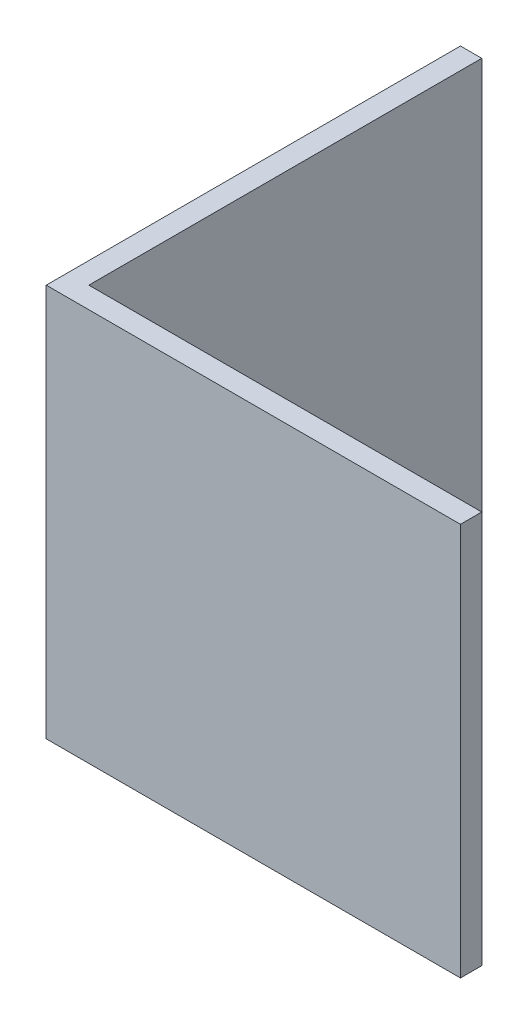
SolidWorks part; units mm, degrees
material "Galvanized Steel"
ref_plane "Front Plane" through (0, 0, 0) normal (0, 0, 1) x (1, 0, 0)
ref_plane "Top Plane" through (0, 0, 0) normal (0, 1, 0) x (1, 0, 0)
ref_plane "Right Plane" through (0, 0, 0) normal (1, 0, 0) x (0, 0, -1)
sketch "Sketch1" plane through (0, 0, 0) normal (0, 1, 0) x (1, 0, 0)
  line L0 (-24.0233, 26.7767) -> (26.7767, 26.7767) construction
  line L1 (-26.7767, -26.7767) -> (26.7767, -26.7767)
  line L2 (-26.7767, -26.7767) -> (-26.7767, 26.7767)
  line L3 (-26.7767, 26.7767) -> (-24.0233, 26.7767)
  line L4 (26.7767, -26.7767) -> (26.7767, -24.0233)
  line L5 (-26.7767, -26.7767) -> (26.7767, 26.7767) construction
  line L6 (-26.7767, 26.7767) -> (26.7767, -26.7767) construction
  line L9 (26.7767, -24.0233) -> (-24.0233, -24.0233)
  line L10 (-24.0233, 26.7767) -> (-24.0233, -24.0233)
  line L11 (26.7767, 26.7767) -> (26.7767, -24.0233) construction
  point P0 (0, 0)
  dimension "D1" = 2.7534
  dimension "D2" = 50.8
extrude "Boss-Extrude1" add sketch "Sketch1" along normal blind 50.8
